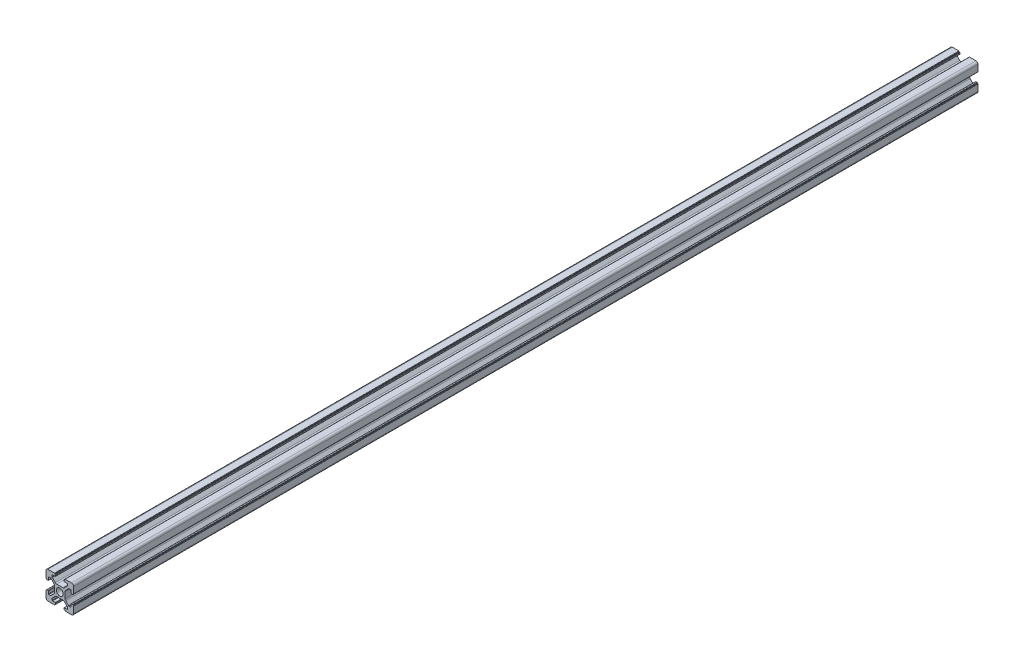
SolidWorks part; units mm, degrees
ref_plane "前视基准面" through (0, 0, 0) normal (0, 0, 1) x (1, 0, 0)
ref_plane "上视基准面" through (0, 0, 0) normal (0, 1, 0) x (1, 0, 0)
ref_plane "右视基准面" through (0, 0, 0) normal (1, 0, 0) x (0, 0, -1)
sketch "草图1" plane through (0, 0, 0) normal (0, 0, 1) x (1, 0, 0)
  line L0 (0, 0) -> (0, 5.5) construction
  line L1 (-8.5023, -10.0023) -> (-3.85, -10.0023)
  line L2 (-10.0023, -8.5023) -> (-10.0023, -3.85)
  line L3 (-8.5023, 10.0023) -> (-3.85, 10.0023)
  line L4 (10.0023, -8.5023) -> (10.0023, -3.85)
  line L5 (-10.0023, -10.0023) -> (10.0023, 10.0023) construction
  line L6 (-10.0023, 10.0023) -> (10.0023, -10.0023) construction
  line L7 (-2.218, -3.9) -> (2.218, -3.9)
  line L8 (-3.9, -2.218) -> (-3.9, 2.218)
  line L9 (-2.218, 3.9) -> (2.218, 3.9)
  line L10 (3.9, -2.218) -> (3.9, 2.218)
  line L11 (-3.9, -3.9) -> (3.9, 3.9) construction
  line L12 (-3.9, 3.9) -> (3.9, -3.9) construction
  line L13 (-5.25, -8.2) -> (-3.35, -8.2)
  line L14 (-8.2, -5.25) -> (-8.2, -3.35)
  line L15 (-5.25, 8.2) -> (-3.35, 8.2)
  line L16 (8.2, -5.25) -> (8.2, -3.35)
  line L17 (-8.2, -8.2) -> (8.2, 8.2) construction
  line L18 (-8.2, 8.2) -> (8.2, -8.2) construction
  line L19 (-7.95, 5.5) -> (-6.6642, 5.5)
  line L20 (0, 0) -> (5.5, 0) construction
  line L23 (-5.5, 7.95) -> (-5.5, 6.6642)
  line L26 (0, 0) -> (-0.5303, 0.5303)
  line L27 (3.2787, 4.3393) -> (5.4268, 6.4874)
  line L28 (0, 0) -> (0.5303, -0.5303)
  line L29 (5.5, 6.6642) -> (5.5, 7.95)
  line L30 (4.3393, 3.2787) -> (6.4874, 5.4268)
  line L31 (6.6642, 5.5) -> (7.95, 5.5)
  line L32 (4.3393, -3.2787) -> (6.4874, -5.4268)
  line L33 (3.2787, -4.3393) -> (5.4268, -6.4874)
  line L34 (-3.2787, -4.3393) -> (-5.4268, -6.4874)
  line L35 (-4.3393, -3.2787) -> (-6.4874, -5.4268)
  line L36 (-4.3393, 3.2787) -> (-6.4874, 5.4268)
  line L37 (-3.2787, 4.3393) -> (-5.4268, 6.4874)
  line L38 (3.1, -8.45) -> (3.1, -9.2523)
  line L39 (8.45, 3.1) -> (9.2523, 3.1)
  line L40 (-5.5, -6.6642) -> (-5.5, -7.95)
  line L41 (-6.6642, -5.5) -> (-7.95, -5.5)
  line L42 (5.5, -6.6642) -> (5.5, -7.95)
  line L43 (6.6642, -5.5) -> (7.95, -5.5)
  line L44 (9.2523, -3.1) -> (8.45, -3.1)
  line L46 (10.0023, 3.85) -> (10.0023, 8.5023)
  line L47 (8.2, 3.35) -> (8.2, 5.25)
  line L48 (-3.1, -9.2523) -> (-3.1, -8.45)
  line L49 (-8.45, -3.1) -> (-9.2523, -3.1)
  line L50 (-9.2523, 3.1) -> (-8.45, 3.1)
  line L51 (-3.1, 8.45) -> (-3.1, 9.2523)
  line L52 (3.1, 9.2523) -> (3.1, 8.45)
  line L53 (3.85, 10.0023) -> (8.5023, 10.0023)
  line L54 (3.35, 8.2) -> (5.25, 8.2)
  line L55 (-10.0023, 3.85) -> (-10.0023, 8.5023)
  line L56 (-8.2, 3.35) -> (-8.2, 5.25)
  line L57 (3.35, -8.2) -> (5.25, -8.2)
  line L58 (3.85, -10.0023) -> (8.5023, -10.0023)
  line L59 (9.7523, -3.6) -> (9.5023, -3.6)
  line L61 (9.7523, 3.6) -> (9.5023, 3.6)
  line L62 (9.5023, -3.6) -> (9.5023, -3.35)
  line L63 (3.6, -9.7523) -> (3.6, -9.5023)
  line L64 (3.35, -9.5023) -> (3.6, -9.5023)
  line L65 (9.5023, 3.35) -> (9.5023, 3.6)
  line L66 (-3.6, -9.5023) -> (-3.35, -9.5023)
  line L67 (-3.6, -9.7523) -> (-3.6, -9.5023)
  line L68 (-9.7523, -3.6) -> (-9.5023, -3.6)
  line L69 (-9.5023, -3.35) -> (-9.5023, -3.6)
  line L70 (-9.5023, 3.6) -> (-9.5023, 3.35)
  line L71 (-9.7523, 3.6) -> (-9.5023, 3.6)
  line L72 (-3.6, 9.7523) -> (-3.6, 9.5023)
  line L73 (-3.35, 9.5023) -> (-3.6, 9.5023)
  line L74 (3.6, 9.5023) -> (3.35, 9.5023)
  line L75 (3.6, 9.7523) -> (3.6, 9.5023)
  circle A0 centre (0, 0) radius 2.5
  arc A1 (10.0023, 8.5023) -> (8.5023, 10.0023) centre (8.5023, 8.5023) ccw
  arc A2 (8.5023, -10.0023) -> (10.0023, -8.5023) centre (8.5023, -8.5023) ccw
  arc A3 (-10.0023, -8.5023) -> (-8.5023, -10.0023) centre (-8.5023, -8.5023) ccw
  arc A4 (-10.0023, 8.5023) -> (-8.5023, 10.0023) centre (-8.5023, 8.5023) cw
  arc A5 (-9.5023, -3.35) -> (-9.2523, -3.1) centre (-9.2523, -3.35) cw
  arc A6 (-9.7523, -3.6) -> (-10.0023, -3.85) centre (-9.7523, -3.85) ccw
  arc A7 (-8.45, -3.1) -> (-8.2, -3.35) centre (-8.45, -3.35) cw
  arc A8 (-7.95, -5.5) -> (-8.2, -5.25) centre (-7.95, -5.25) cw
  arc A9 (-6.4874, -5.4268) -> (-6.6642, -5.5) centre (-6.6642, -5.25) cw
  arc A10 (-5.4268, -6.4874) -> (-5.5, -6.6642) centre (-5.25, -6.6642) ccw
  arc A11 (-5.5, -7.95) -> (-5.25, -8.2) centre (-5.25, -7.95) ccw
  arc A12 (-3.6, -9.7523) -> (-3.85, -10.0023) centre (-3.85, -9.7523) cw
  arc A13 (-3.35, -9.5023) -> (-3.1, -9.2523) centre (-3.35, -9.2523) ccw
  arc A14 (-3.1, -8.45) -> (-3.35, -8.2) centre (-3.35, -8.45) ccw
  arc A15 (3.1, -8.45) -> (3.35, -8.2) centre (3.35, -8.45) cw
  arc A16 (5.5, -7.95) -> (5.25, -8.2) centre (5.25, -7.95) cw
  arc A17 (5.4268, -6.4874) -> (5.5, -6.6642) centre (5.25, -6.6642) cw
  arc A18 (6.4874, -5.4268) -> (6.6642, -5.5) centre (6.6642, -5.25) ccw
  arc A19 (7.95, -5.5) -> (8.2, -5.25) centre (7.95, -5.25) ccw
  arc A20 (8.45, -3.1) -> (8.2, -3.35) centre (8.45, -3.35) ccw
  arc A21 (9.5023, -3.35) -> (9.2523, -3.1) centre (9.2523, -3.35) ccw
  arc A22 (9.7523, -3.6) -> (10.0023, -3.85) centre (9.7523, -3.85) cw
  arc A23 (3.35, -9.5023) -> (3.1, -9.2523) centre (3.35, -9.2523) cw
  arc A24 (3.6, -9.7523) -> (3.85, -10.0023) centre (3.85, -9.7523) ccw
  arc A25 (7.95, 5.5) -> (8.2, 5.25) centre (7.95, 5.25) cw
  arc A26 (8.2, 3.35) -> (8.45, 3.1) centre (8.45, 3.35) ccw
  arc A27 (9.5023, 3.35) -> (9.2523, 3.1) centre (9.2523, 3.35) cw
  arc A28 (9.7523, 3.6) -> (10.0023, 3.85) centre (9.7523, 3.85) ccw
  arc A29 (6.6642, 5.5) -> (6.4874, 5.4268) centre (6.6642, 5.25) ccw
  arc A30 (5.4268, 6.4874) -> (5.5, 6.6642) centre (5.25, 6.6642) ccw
  arc A31 (5.5, 7.95) -> (5.25, 8.2) centre (5.25, 7.95) ccw
  arc A32 (3.1, 8.45) -> (3.35, 8.2) centre (3.35, 8.45) ccw
  arc A33 (3.6, 9.7523) -> (3.85, 10.0023) centre (3.85, 9.7523) cw
  arc A34 (3.35, 9.5023) -> (3.1, 9.2523) centre (3.35, 9.2523) ccw
  arc A35 (-9.7523, 3.6) -> (-10.0023, 3.85) centre (-9.7523, 3.85) cw
  arc A36 (-9.5023, 3.35) -> (-9.2523, 3.1) centre (-9.2523, 3.35) ccw
  arc A37 (-8.45, 3.1) -> (-8.2, 3.35) centre (-8.45, 3.35) ccw
  arc A38 (-8.2, 5.25) -> (-7.95, 5.5) centre (-7.95, 5.25) cw
  arc A39 (-6.4874, 5.4268) -> (-6.6642, 5.5) centre (-6.6642, 5.25) ccw
  arc A40 (-5.4268, 6.4874) -> (-5.5, 6.6642) centre (-5.25, 6.6642) cw
  arc A41 (-5.5, 7.95) -> (-5.25, 8.2) centre (-5.25, 7.95) cw
  arc A42 (-3.1, 8.45) -> (-3.35, 8.2) centre (-3.35, 8.45) cw
  arc A43 (-3.1, 9.2523) -> (-3.35, 9.5023) centre (-3.35, 9.2523) ccw
  arc A44 (-3.6, 9.7523) -> (-3.85, 10.0023) centre (-3.85, 9.7523) ccw
  arc A45 (-4.3393, 3.2787) -> (-3.9, 2.218) centre (-5.4, 2.218) cw
  arc A46 (-3.2787, 4.3393) -> (-2.218, 3.9) centre (-2.218, 5.4) ccw
  arc A47 (3.2787, 4.3393) -> (2.218, 3.9) centre (2.218, 5.4) cw
  arc A48 (4.3393, 3.2787) -> (3.9, 2.218) centre (5.4, 2.218) ccw
  arc A49 (4.3393, -3.2787) -> (3.9, -2.218) centre (5.4, -2.218) cw
  arc A50 (3.2787, -4.3393) -> (2.218, -3.9) centre (2.218, -5.4) ccw
  arc A51 (-4.3393, -3.2787) -> (-3.9, -2.218) centre (-5.4, -2.218) ccw
  arc A52 (-2.218, -3.9) -> (-3.2787, -4.3393) centre (-2.218, -5.4) ccw
  point P0 (0, 0)
  point P7 (10.0023, 0)
  point P62 (0, 0)
  point P76 (0, 0)
  point P92 (-8.2, -5.5)
  point P99 (0, 0)
  point P106 (-5.5, -8.2)
  point P117 (5.5, -8.2)
  point P124 (8.2, -5.5)
  point P137 (8.2, 5.5)
  point P140 (8.2, 3.1)
  point P147 (6.5607, 5.5)
  point P152 (5.5, 8.2)
  point P167 (-8.2, 5.5)
  point P174 (-5.5, 8.2)
  dimension "D1" = 1.5
  dimension "D5" = 0.25
  dimension "D6" = 1.5
  dimension "D2" = 4
  dimension "D3" = 4
  dimension "D4" = 4
extrude "凸台-拉伸1" add sketch "草图1" along normal blind 656 contours A52 L7 A50 L33 A17 L42 A16 L57 A15 L38 A23 L64 L63 A24 L58 A2 L4 A22 L59 L62 A21 L44 A20 L16 A19 L43 A18 L32 A49 L10 A48 L30 A29 L31 A25 L47 A26 L39 A27 L65 L61 A28 L46 A1 L53 A33 L75 L74 A34 L52 A32
